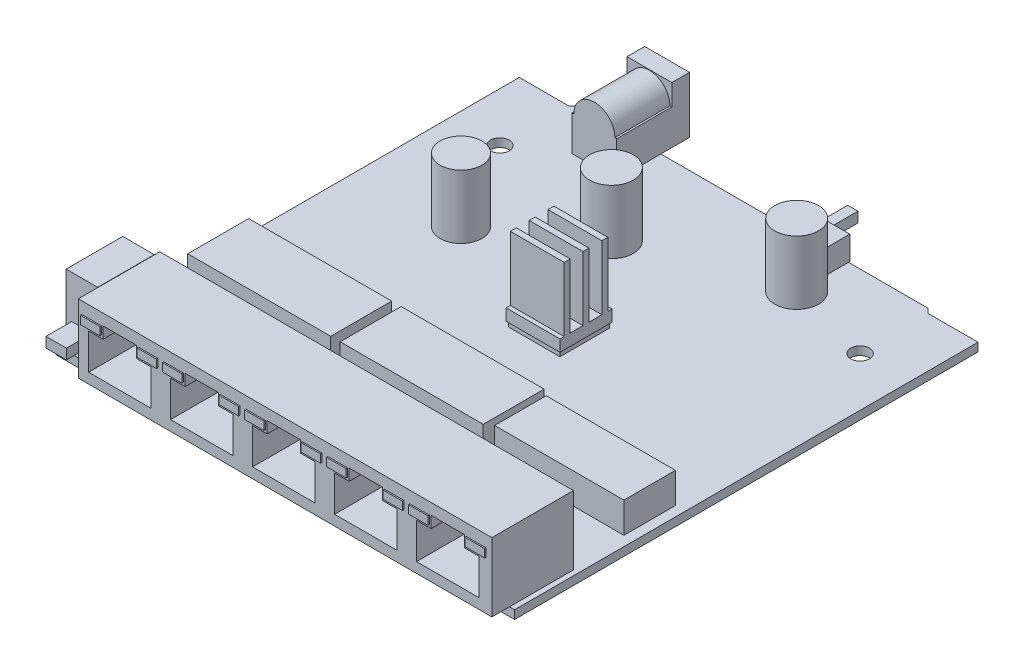
SolidWorks part; units mm, degrees
ref_plane "Front Plane" through (0, 0, 0) normal (0, 0, 1) x (1, 0, 0)
ref_plane "Top Plane" through (0, 0, 0) normal (0, 1, 0) x (1, 0, 0)
ref_plane "Right Plane" through (0, 0, 0) normal (1, 0, 0) x (0, 0, -1)
sketch "Sketch1" plane through (0, 0, 0) normal (0, 1, 0) x (1, 0, 0)
  line L0 (44.75, 44.78) -> (35, 44.78)
  line L1 (44.75, -45.65) -> (-44.75, -45.65)
  line L2 (44.75, -45.65) -> (44.75, 44.78)
  line L3 (34.13, 45.65) -> (-34.13, 45.65)
  line L4 (-44.75, -45.65) -> (-44.75, 44.78)
  line L5 (0, 0) -> (35, 0) construction
  line L7 (35, 44.78) -> (34.13, 45.65)
  line L8 (0, 0) -> (0, 45.65) construction
  line L9 (-44.75, 44.78) -> (-35, 44.78)
  line L10 (-35, 44.78) -> (-34.13, 45.65)
  point P0 (0, 0)
  dimension "D1" = 89.5
  dimension "D2" = 91.3
  dimension "D3" = 0.87
  dimension "D4" = 45
  dimension "D5" = 70
extrude "Boss-Extrude1" add sketch "Sketch1" along normal blind 1.65
sketch "Sketch3" plane through (0, 1.65, 0) normal (0, 1, 0) x (1, 0, 0)
  line L0 (44.75, -45.65) -> (44.75, 44.78) construction
  line L1 (43.75, -49.07) -> (-36.95, -49.07)
  line L2 (43.75, -49.07) -> (43.75, -33.17)
  line L3 (43.75, -33.17) -> (-36.95, -33.17)
  line L4 (-36.95, -49.07) -> (-36.95, -33.17)
  line L5 (-44.75, -45.65) -> (44.75, -45.65) construction
  dimension "D1" = 1
  dimension "D2" = 15.9
  dimension "D3" = 3.42
  dimension "D4" = 80.7
extrude "Boss-Extrude2" add sketch "Sketch3" along normal blind 13.41
sketch "Sketch4" plane through (0, 1.65, 0) normal (0, 1, 0) x (1, 0, 0)
  line L0 (44.75, -45.65) -> (44.75, 44.78) construction
  line L1 (44.75, 44.78) -> (35, 44.78) construction
  line L2 (0, 0) -> (0, 45.65) construction
  line L3 (34.13, 45.65) -> (-34.13, 45.65) construction
  circle A0 centre (35.15, 31.38) radius 1.825
  circle A1 centre (-35.15, 31.38) radius 1.825
  dimension "D3" = 3.65
  dimension "D1" = 9.6
  dimension "D2" = 13.4
extrude "Cut-Extrude1" cut sketch "Sketch4" against normal through all
sketch "Sketch5" plane through (0, 1.65, 0) normal (0, 1, 0) x (1, 0, 0)
  line L0 (-44.75, -45.65) -> (-36.95, -45.65) construction
  line L1 (-44.25, -44.15) -> (-38.1, -44.15)
  line L2 (-44.25, -44.15) -> (-44.25, -33.1)
  line L3 (-44.25, -33.1) -> (-38.1, -33.1)
  line L4 (-38.1, -44.15) -> (-38.1, -33.1)
  line L5 (-44.75, 44.78) -> (-44.75, -45.65) construction
  dimension "D1" = 6.15
  dimension "D2" = 11.05
  dimension "D3" = 1.5
  dimension "D4" = 0.5
extrude "Boss-Extrude3" add sketch "Sketch5" along normal blind 12.32
sketch "Sketch6" plane through (0, 0, 44.15) normal (0, 0, 1) x (1, 0, 0)
  line L0 (-41.175, 13.97) -> (-41.175, 1.65) construction
  line L1 (-39.175, 3.65) -> (-43.175, 3.65)
  line L2 (-39.175, 3.65) -> (-39.175, 5.65)
  line L3 (-39.175, 5.65) -> (-43.175, 5.65)
  line L4 (-43.175, 3.65) -> (-43.175, 5.65)
  line L5 (-39.175, 3.65) -> (-43.175, 5.65) construction
  line L6 (-39.175, 5.65) -> (-43.175, 3.65) construction
  line L7 (-44.25, 13.97) -> (-38.1, 13.97) construction
  line L8 (-44.25, 1.65) -> (-38.1, 1.65) construction
  line L9 (-44.75, 1.65) -> (-36.95, 1.65) construction
  point P0 (-41.175, 4.65)
  dimension "D1" = 2
  dimension "D2" = 4
  dimension "D3" = 2
extrude "Boss-Extrude4" add sketch "Sketch6" along normal blind 5
sketch "Sketch7" plane through (0, 0, 49.07) normal (0, 0, 1) x (1, 0, 0)
  line L0 (-28.85, 10.65) -> (-28.85, 3.65) construction
  line L1 (-34.95, 3.65) -> (-22.75, 3.65)
  line L2 (-34.95, 3.65) -> (-34.95, 10.65)
  line L3 (-34.95, 10.65) -> (-22.75, 10.65)
  line L4 (-22.75, 3.65) -> (-22.75, 10.65)
  line L6 (-32.1, 10.65) -> (-32.1, 12.9)
  line L7 (-32.1, 12.9) -> (-25.6, 12.9)
  line L8 (-25.6, 10.65) -> (-25.6, 12.9)
  line L9 (-36.95, 1.65) -> (43.75, 1.65) construction
  line L10 (-36.95, 15.06) -> (-36.95, 1.65) construction
  line L11 (-18.95, 3.65) -> (-6.75, 3.65)
  line L12 (-6.75, 3.65) -> (-6.75, 10.65)
  line L13 (-18.95, 10.65) -> (-6.75, 10.65)
  line L14 (-9.6, 10.65) -> (-9.6, 12.9)
  line L15 (-16.1, 12.9) -> (-9.6, 12.9)
  line L16 (-16.1, 10.65) -> (-16.1, 12.9)
  line L17 (-18.95, 3.65) -> (-18.95, 10.65)
  line L18 (-2.95, 3.65) -> (9.25, 3.65)
  line L19 (9.25, 3.65) -> (9.25, 10.65)
  line L20 (-2.95, 10.65) -> (9.25, 10.65)
  line L21 (6.4, 10.65) -> (6.4, 12.9)
  line L22 (-0.1, 12.9) -> (6.4, 12.9)
  line L23 (-0.1, 10.65) -> (-0.1, 12.9)
  line L24 (-2.95, 3.65) -> (-2.95, 10.65)
  line L25 (13.05, 3.65) -> (25.25, 3.65)
  line L26 (25.25, 3.65) -> (25.25, 10.65)
  line L27 (13.05, 10.65) -> (25.25, 10.65)
  line L28 (22.4, 10.65) -> (22.4, 12.9)
  line L29 (15.9, 12.9) -> (22.4, 12.9)
  line L30 (15.9, 10.65) -> (15.9, 12.9)
  line L31 (13.05, 3.65) -> (13.05, 10.65)
  line L32 (29.05, 3.65) -> (41.25, 3.65)
  line L33 (41.25, 3.65) -> (41.25, 10.65)
  line L34 (29.05, 10.65) -> (41.25, 10.65)
  line L35 (38.4, 10.65) -> (38.4, 12.9)
  line L36 (31.9, 12.9) -> (38.4, 12.9)
  line L37 (31.9, 10.65) -> (31.9, 12.9)
  line L38 (29.05, 3.65) -> (29.05, 10.65)
  line L39 (-34.95, 3.65) -> (-18.95, 3.65) construction
  dimension "D1" = 12.2
  dimension "D2" = 7
  dimension "D3" = 2
  dimension "D4" = 2
  dimension "D5" = 2.25
  dimension "D6" = 6.5
  dimension "D8" = 16
  dimension "D7" = 5
extrude "Cut-Extrude2" cut sketch "Sketch7" against normal blind 11.55 contours L3 L8 L7 L6 | L3 L0 L1 L4 | L0 L3 L2 L1 | L17 L11 L12 L13 | L16 L13 L14 L15 | L24 L18 L19 L20 | L23 L20 L21 L22 | L31 L25 L26 L27 | L30 L27 L28 L29 | L38 L32 L33 L34 | L37 L34 L35 L36
sketch "Sketch8" plane through (0, 1.65, 0) normal (0, 1, 0) x (1, 0, 0)
  line L0 (-44.75, 44.78) -> (-44.75, -45.65) construction
  line L1 (-41.35, -23.32) -> (-13.45, -23.32)
  line L2 (-41.35, -23.32) -> (-41.35, -11.42)
  line L3 (-41.35, -11.42) -> (-13.45, -11.42)
  line L4 (-13.45, -23.32) -> (-13.45, -11.42)
  line L5 (-11.6, -23.32) -> (16.3, -23.32)
  line L6 (-11.6, -23.32) -> (-11.6, -11.42)
  line L7 (-11.6, -11.42) -> (16.3, -11.42)
  line L8 (16.3, -23.32) -> (16.3, -11.42)
  line L9 (17.61, -22.395) -> (42.83, -22.395)
  line L10 (17.61, -22.395) -> (17.61, -12.345)
  line L11 (17.61, -12.345) -> (42.83, -12.345)
  line L12 (42.83, -22.395) -> (42.83, -12.345)
  line L13 (43.75, -33.17) -> (-36.95, -33.17) construction
  line L14 (44.75, -45.65) -> (44.75, 44.78) construction
  line L15 (16.3, -17.37) -> (-11.6, -17.37) construction
  dimension "D1" = 3.4
  dimension "D2" = 11.9
  dimension "D3" = 27.9
  dimension "D4" = 1.85
  dimension "D5" = 9.85
  dimension "D6" = 25.22
  dimension "D7" = 10.05
  dimension "D8" = 1.92
extrude "Boss-Extrude5" add sketch "Sketch8" along normal blind 5.95
sketch "Sketch9" plane through (0, 1.65, 0) normal (0, 1, 0) x (1, 0, 0)
  line L0 (44.75, -45.65) -> (44.75, 44.78) construction
  line L1 (-3.58, 1.54) -> (6.42, 1.54)
  line L2 (-3.58, 1.54) -> (-3.58, 11.2)
  line L3 (-3.58, 11.2) -> (6.42, 11.2)
  line L4 (6.42, 1.54) -> (6.42, 11.2)
  line L5 (34.13, 45.65) -> (-34.13, 45.65) construction
  dimension "D1" = 9.66
  dimension "D2" = 10
  dimension "D3" = 38.33
  dimension "D4" = 34.45
extrude "Boss-Extrude6" add sketch "Sketch9" along normal blind 1
sketch "Sketch10" plane through (0, 2.65, 0) normal (0, 1, 0) x (1, 0, 0)
  line L14 (-3.83, 1.29) -> (6.67, 1.29)
  line L15 (6.67, 1.29) -> (6.67, 11.45)
  line L16 (6.67, 11.45) -> (-3.83, 11.45)
  line L17 (-3.83, 11.45) -> (-3.83, 1.29)
  line L18 (-3.83, 1.29) -> (6.67, 1.29)
  line L19 (6.67, 1.29) -> (6.67, 11.45)
  line L20 (6.67, 11.45) -> (-3.83, 11.45)
  line L21 (-3.83, 11.45) -> (-3.83, 1.29)
  dimension "D1" = 0.25
extrude "Boss-Extrude7" add sketch "Sketch10" along normal blind 14.78
sketch "Sketch11" plane through (-3.83, 0, 0) normal (-1, 0, 0) x (0, 0, 1)
  line L0 (-11.45, 17.43) -> (-1.29, 17.43) construction
  line L1 (-9.455, 17.43) -> (-6.955, 17.43)
  line L2 (-9.455, 17.43) -> (-9.455, 4.91)
  line L3 (-9.455, 4.91) -> (-6.955, 4.91)
  line L4 (-6.955, 17.43) -> (-6.955, 4.91)
  line L5 (-6.37, 17.43) -> (-6.37, 2.65) construction
  line L6 (-5.785, 17.43) -> (-3.285, 17.43)
  line L7 (-5.785, 17.43) -> (-5.785, 4.91)
  line L8 (-5.785, 4.91) -> (-3.285, 4.91)
  line L9 (-3.285, 17.43) -> (-3.285, 4.91)
  line L10 (-11.2, 2.65) -> (-1.54, 2.65) construction
  line L11 (-10.625, 17.43) -> (-10.625, 4.91)
  line L12 (-10.625, 4.91) -> (-11.45, 4.91)
  line L13 (-11.45, 17.43) -> (-11.45, 2.65) construction
  line L14 (-11.45, 4.91) -> (-11.45, 17.43)
  line L15 (-11.45, 17.43) -> (-10.625, 17.43)
  line L16 (-1.29, 4.91) -> (-1.29, 17.43)
  line L17 (-2.115, 4.91) -> (-1.29, 4.91)
  line L18 (-2.115, 17.43) -> (-2.115, 4.91)
  line L19 (-1.29, 17.43) -> (-2.115, 17.43)
  dimension "D1" = 2.5
  dimension "D2" = 12.52
  dimension "D3" = 1.17
  dimension "D4" = 1.17
extrude "Cut-Extrude3" cut sketch "Sketch11" against normal up to next
sketch "Sketch12" plane through (0, 1.65, 0) normal (0, 1, 0) x (1, 0, 0)
  line L0 (34.13, 45.65) -> (-34.13, 45.65) construction
  line L1 (44.75, -45.65) -> (44.75, 44.78) construction
  line L2 (-44.75, 44.78) -> (-44.75, -45.65) construction
  circle A0 centre (18.5, 35.65) radius 4.275
  circle A1 centre (-8.15, 26.15) radius 4.275
  circle A2 centre (-25.25, 13.9) radius 4.085
  point P10 (-0.0735, 50.8837)
  dimension "D3" = 8.55
  dimension "D4" = 8.17
  dimension "D1" = 10
  dimension "D2" = 26.25
  dimension "D5" = 19.5
  dimension "D6" = 36.6
  dimension "D7" = 19.5
  dimension "D8" = 31.75
extrude "Boss-Extrude8" add sketch "Sketch12" along normal blind 12.4
sketch "Sketch14" plane through (0, 1.65, 0) normal (0, 1, 0) x (1, 0, 0)
  line L0 (34.13, 45.65) -> (-34.13, 45.65) construction
  line L1 (-26.75, 51.24) -> (-18, 51.24)
  line L2 (-26.75, 51.24) -> (-26.75, 37.04)
  line L3 (-26.75, 37.04) -> (-18, 37.04)
  line L4 (-18, 51.24) -> (-18, 37.04)
  line L5 (-44.75, 44.78) -> (-44.75, -45.65) construction
  dimension "D1" = 8.75
  dimension "D2" = 14.2
  dimension "D3" = 5.59
  dimension "D4" = 18
extrude "Boss-Extrude9" add sketch "Sketch14" along normal blind 11
sketch "Sketch15" plane through (0, 0, -51.24) normal (0, 0, -1) x (-1, 0, 0)
  line L0 (22.375, 12.65) -> (22.375, 1.65) construction
  line L1 (18, 12.65) -> (26.75, 12.65) construction
  line L2 (18, 1.65) -> (26.75, 1.65) construction
  circle A0 centre (22.375, 8.5333) radius 3.1
  circle A1 centre (22.375, 8.5333) radius 0.8
  dimension "D1" = 6.2
  dimension "D2" = 1.6
extrude "Cut-Extrude4" cut sketch "Sketch15" against normal blind 9.92
sketch "Sketch17" plane through (0, 0, -37.04) normal (0, 0, 1) x (1, 0, 0)
  line L0 (-26.375, 8.5333) -> (-26.75, 8.5333)
  line L1 (-26.75, 12.65) -> (-26.75, 1.65) construction
  line L2 (-26.75, 8.5333) -> (-26.75, 12.65)
  line L3 (-26.75, 12.65) -> (-18, 12.65)
  line L4 (-18, 12.65) -> (-18, 8.5333)
  line L5 (-18, 12.65) -> (-18, 1.65) construction
  line L6 (-18, 8.5333) -> (-18.375, 8.5333)
  circle A0 centre (-22.375, 8.5333) radius 3.1 construction
  circle A1 centre (-22.375, 8.5333) radius 3.1 construction
  arc A2 (-18.375, 8.5333) -> (-26.375, 8.5333) centre (-22.375, 8.5333) ccw
  dimension "D1" = 8
extrude "Cut-Extrude5" cut sketch "Sketch17" against normal offset from surface (10.75 mm away) 3.45 up to face at (-25.475, 8.5333, -51.24)
sketch "Sketch18" plane through (0, 1.65, 0) normal (0, 1, 0) x (1, 0, 0)
  line L0 (34.13, 45.65) -> (-18, 45.65) construction
  line L1 (9.97, 45.9) -> (18.62, 45.9)
  line L2 (9.97, 45.9) -> (9.97, 41.49)
  line L3 (9.97, 41.49) -> (18.62, 41.49)
  line L4 (18.62, 45.9) -> (18.62, 41.49)
  line L5 (44.75, -45.65) -> (44.75, 44.78) construction
  dimension "D1" = 8.65
  dimension "D2" = 4.41
  dimension "D3" = 0.25
  dimension "D4" = 26.13
extrude "Boss-Extrude10" add sketch "Sketch18" along normal blind 4.64
sketch "Sketch19" plane through (0, 0, -45.9) normal (0, 0, -1) x (-1, 0, 0)
  line L0 (-18.62, 3.97) -> (-9.97, 3.97) construction
  line L1 (-18.62, 6.29) -> (-18.62, 1.65) construction
  line L2 (-9.97, 6.29) -> (-9.97, 1.65) construction
  line L4 (-14.22, 2.97) -> (-12.22, 2.97)
  line L5 (-14.22, 2.97) -> (-14.22, 4.97)
  line L6 (-14.22, 4.97) -> (-12.22, 4.97)
  line L7 (-12.22, 2.97) -> (-12.22, 4.97)
  line L8 (-14.22, 2.97) -> (-12.22, 4.97) construction
  line L9 (-14.22, 4.97) -> (-12.22, 2.97) construction
  point P6 (-13.22, 3.97)
  dimension "D1" = 2
  dimension "D2" = 2.25
extrude "Boss-Extrude11" add sketch "Sketch19" along normal blind 6
sketch "Sketch20" plane through (0, 0, 49.07) normal (0, 0, 1) x (1, 0, 0)
  line L0 (-28.85, 12.9) -> (-28.85, 3.65) construction
  line L1 (-32.465, 11.15) -> (-36.265, 11.15)
  line L2 (-32.465, 11.15) -> (-32.465, 12.75)
  line L3 (-32.465, 12.75) -> (-36.265, 12.75)
  line L4 (-36.265, 11.15) -> (-36.265, 12.75)
  line L5 (-32.1, 12.9) -> (-25.6, 12.9) construction
  line L6 (-34.95, 3.65) -> (-22.75, 3.65) construction
  line L7 (-34.95, 10.65) -> (-32.1, 10.65) construction
  line L8 (-25.235, 11.15) -> (-25.235, 12.75)
  line L9 (-25.235, 12.75) -> (-21.435, 12.75)
  line L10 (-21.435, 11.15) -> (-21.435, 12.75)
  line L11 (-25.235, 11.15) -> (-21.435, 11.15)
  line L12 (-9.235, 12.75) -> (-5.435, 12.75)
  line L13 (-9.235, 11.15) -> (-9.235, 12.75)
  line L14 (-9.235, 11.15) -> (-5.435, 11.15)
  line L15 (-5.435, 11.15) -> (-5.435, 12.75)
  line L16 (-16.465, 12.75) -> (-20.265, 12.75)
  line L17 (-16.465, 11.15) -> (-20.265, 11.15)
  line L18 (-20.265, 11.15) -> (-20.265, 12.75)
  line L19 (-16.465, 11.15) -> (-16.465, 12.75)
  line L20 (6.765, 12.75) -> (10.565, 12.75)
  line L21 (6.765, 11.15) -> (6.765, 12.75)
  line L22 (6.765, 11.15) -> (10.565, 11.15)
  line L23 (10.565, 11.15) -> (10.565, 12.75)
  line L24 (-0.465, 12.75) -> (-4.265, 12.75)
  line L25 (-0.465, 11.15) -> (-4.265, 11.15)
  line L26 (-4.265, 11.15) -> (-4.265, 12.75)
  line L27 (-0.465, 11.15) -> (-0.465, 12.75)
  line L28 (22.765, 12.75) -> (26.565, 12.75)
  line L29 (22.765, 11.15) -> (22.765, 12.75)
  line L30 (22.765, 11.15) -> (26.565, 11.15)
  line L31 (26.565, 11.15) -> (26.565, 12.75)
  line L32 (15.535, 12.75) -> (11.735, 12.75)
  line L33 (15.535, 11.15) -> (11.735, 11.15)
  line L34 (11.735, 11.15) -> (11.735, 12.75)
  line L35 (15.535, 11.15) -> (15.535, 12.75)
  line L36 (38.765, 12.75) -> (42.565, 12.75)
  line L37 (38.765, 11.15) -> (38.765, 12.75)
  line L38 (38.765, 11.15) -> (42.565, 11.15)
  line L39 (42.565, 11.15) -> (42.565, 12.75)
  line L40 (31.535, 12.75) -> (27.735, 12.75)
  line L41 (31.535, 11.15) -> (27.735, 11.15)
  line L42 (27.735, 11.15) -> (27.735, 12.75)
  line L43 (31.535, 11.15) -> (31.535, 12.75)
  line L44 (-25.235, 12.75) -> (-9.235, 12.75) construction
  dimension "D1" = 1.6
  dimension "D2" = 3.8
  dimension "D3" = 7.23
  dimension "D4" = 0.5
  dimension "D6" = 16
  dimension "D5" = 5
extrude "Boss-Extrude12" add sketch "Sketch20" along normal blind 0.25
